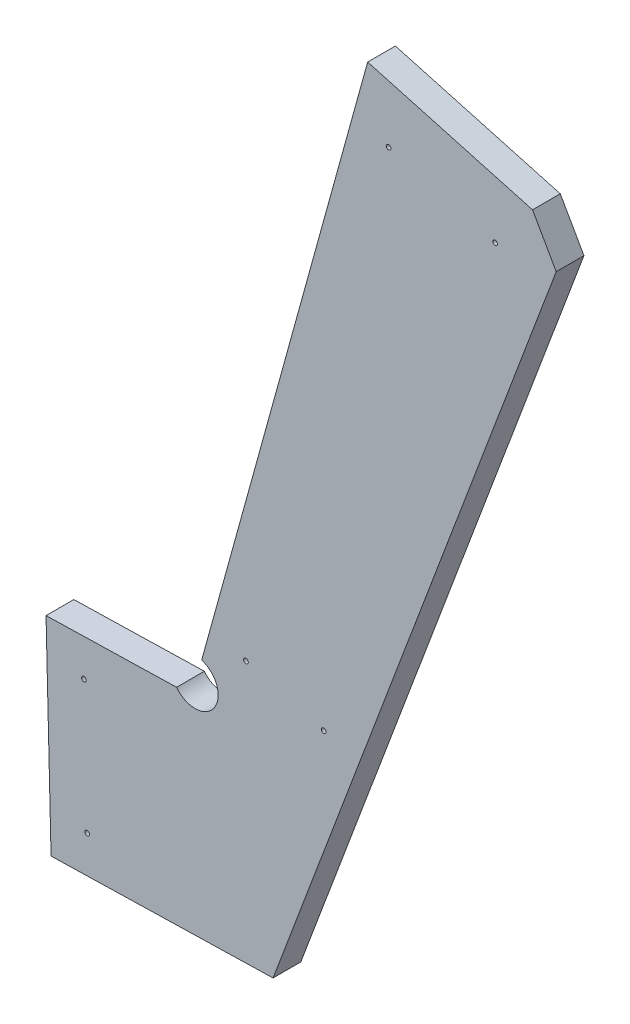
SolidWorks part; units mm, degrees
material "Beech"
ref_plane "Front Plane" through (0, 0, 0) normal (0, 0, 1) x (1, 0, 0)
ref_plane "Top Plane" through (0, 0, 0) normal (0, 1, 0) x (1, 0, 0)
ref_plane "Right Plane" through (0, 0, 0) normal (1, 0, 0) x (0, 0, -1)
sketch "Sketch1" plane through (0, 0, 0) normal (0, 0, 1) x (1, 0, 0)
  line L0 (-45.6457, -462.2836) -> (-42.1969, -603.5294)
  line L12 (288.249, -54.1429) -> (175.0934, -22.8896)
  line L13 (175.0934, -22.8896) -> (61.1778, -435.3327)
  line L14 (43.9506, -460.0959) -> (-45.6457, -462.2836)
  line L16 (-42.1969, -603.5294) -> (110.1577, -599.8093)
  line L17 (110.1577, -599.8093) -> (304.502, -82.7999)
  line L37 (304.502, -82.7999) -> (288.249, -54.1429)
  arc A2 (43.9506, -460.0959) -> (61.1778, -435.3327) centre (56.6289, -450.542) ccw
  dimension "D2" = 152.4
extrude "Boss-Extrude1" add sketch "Sketch1" along normal blind 19.05
hole_wizard "Hole1" positions "Sketch2" profile "Sketch3" legacy
sketch "Sketch2" plane through (162.2459, -21.7021, -146.425) normal (-0.9639, 0.2662, 0) x (0, 0, -1)
  line L8 (155.95, -2.2757) -> (155.95, 437.7664) construction
  line L11 (175, -2.2757) -> (175, 437.7664) construction
  line L15 (155.95, -2.2757) -> (155.95, 107.7348)
  line L16 (155.95, 107.7348) -> (155.95, 217.7454)
  line L17 (155.95, 217.7454) -> (155.95, 327.7559)
  line L18 (155.95, 327.7559) -> (155.95, 437.7664)
  line L20 (175, -2.2757) -> (175, 85.7327)
  line L21 (175, 85.7327) -> (175, 173.7411)
  line L22 (175, 173.7411) -> (175, 261.7496)
  line L23 (175, 261.7496) -> (175, 349.758)
  line L24 (175, 349.758) -> (175, 437.7664)
  line L25 (0, 155.0243) -> (0, 437.7664) construction
  point P36 (155.95, 107.7348)
  point P40 (155.95, 327.7559)
  point P46 (175, 85.7327)
  point P52 (175, 349.758)
  point P77 (-175, 349.758)
  point P80 (-175, 85.7327)
  point P81 (-155.95, 327.7559)
  point P83 (-155.95, 107.7348)
sketch "Sketch3" plane through (133.5638, -125.5487, 9.525) normal (0, 0, 1) x (-0.2662, -0.9639, 0)
  line L0 (0, 0) -> (0, 32.7039)
  line L1 (0, 32.7039) -> (1.5875, 31.75)
  line L2 (1.5875, 31.75) -> (1.5875, 4.0177)
  line L3 (1.5875, 4.0177) -> (5.08, 0)
  line L4 (5.08, 0) -> (0, 0)
  line L5 (0, -14.3089) -> (0, 102.4216) construction
  line L6 (0, 32.7039) -> (-1.5875, 31.75) construction
  line L7 (-1.5875, 4.0177) -> (-5.08, 0) construction
  dimension "Diameter" = 3.175
  dimension "Depth" = 31.75
  dimension "C-Sink Diameter" = 10.16
  dimension "C-Sink Angle" = 82
  dimension "Drill Angle" = 118
hole_wizard "Hole2" positions "Sketch4" profile "Sketch5" legacy
sketch "Sketch4" plane through (162.2459, -21.7021, 165.475) normal (-0.9639, 0.2662, 0) x (0, 0, -1)
  line L8 (155.95, -2.2757) -> (155.95, 437.7664) construction
  line L11 (175, -2.2757) -> (175, 437.7664) construction
  line L15 (155.95, -2.2757) -> (155.95, 107.7348)
  line L16 (155.95, 107.7348) -> (155.95, 217.7454)
  line L17 (155.95, 217.7454) -> (155.95, 327.7559)
  line L18 (155.95, 327.7559) -> (155.95, 437.7664)
  line L20 (175, -2.2757) -> (175, 85.7327)
  line L21 (175, 85.7327) -> (175, 173.7411)
  line L22 (175, 173.7411) -> (175, 261.7496)
  line L23 (175, 261.7496) -> (175, 349.758)
  line L24 (175, 349.758) -> (175, 437.7664)
  line L25 (0, 155.0243) -> (0, 437.7664) construction
  point P36 (155.95, 107.7348)
  point P40 (155.95, 327.7559)
  point P46 (175, 85.7327)
  point P52 (175, 349.758)
  point P77 (-175, 349.758)
  point P80 (-175, 85.7327)
  point P81 (-155.95, 327.7559)
  point P83 (-155.95, 107.7348)
sketch "Sketch5" plane through (133.5638, -125.5487, 321.425) normal (0, 0, 1) x (-0.2662, -0.9639, 0)
  line L0 (0, 0) -> (0, 32.7039)
  line L1 (0, 32.7039) -> (1.5875, 31.75)
  line L2 (1.5875, 31.75) -> (1.5875, 4.0177)
  line L3 (1.5875, 4.0177) -> (5.08, 0)
  line L4 (5.08, 0) -> (0, 0)
  line L5 (0, -14.3089) -> (0, 102.4216) construction
  line L6 (0, 32.7039) -> (-1.5875, 31.75) construction
  line L7 (-1.5875, 4.0177) -> (-5.08, 0) construction
  dimension "Diameter" = 3.175
  dimension "Depth" = 31.75
  dimension "C-Sink Diameter" = 10.16
  dimension "C-Sink Angle" = 82
  dimension "Drill Angle" = 118
hole_wizard "Hole3" positions "Sketch6" profile "Sketch7" legacy
sketch "Sketch6" plane through (311.9283, -63.0439, -19.05) normal (0, 0, -1) x (-0.3519, -0.9361, 0)
  line L0 (48.5061, 138.7859) -> (35.9701, 0) construction
  line L5 (414.5728, 105.7206) -> (405.0235, 0) construction
  line L7 (490.0108, 170.6797) -> (621.0107, 117.7523) construction
  line L12 (503.094, 203.0616) -> (634.0938, 150.1342) construction
  line L16 (586.8736, 410.4234) -> (717.8734, 357.496) construction
  line L19 (597.4602, 127.2674) -> (610.5433, 159.6493) construction
  line L20 (610.5433, 159.6493) -> (694.3229, 367.011) construction
  line L22 (513.5613, 161.1647) -> (526.6445, 193.5466) construction
  line L23 (526.6445, 193.5466) -> (610.424, 400.9084) construction
  point P0 (46.2211, 113.4889)
  point P2 (39.3976, 37.9455)
  point P4 (412.2879, 80.4236)
  point P51 (407.3085, 25.297)
  point P56 (513.5613, 161.1647)
  point P58 (597.4602, 127.2674)
  point P61 (610.5433, 159.6493)
  point P63 (694.3229, 367.011)
  point P66 (526.6445, 193.5466)
  point P68 (610.424, 400.9084)
sketch "Sketch7" plane through (189.4334, -66.3768, -19.05) normal (1, 0, 0) x (0, 1, 0)
  line L0 (0, 0) -> (0, 39.0539)
  line L1 (0, 39.0539) -> (1.5875, 38.1)
  line L2 (1.5875, 38.1) -> (1.5875, 4.0177)
  line L3 (1.5875, 4.0177) -> (5.08, 0)
  line L4 (5.08, 0) -> (0, 0)
  line L5 (0, -14.3089) -> (0, 102.4216) construction
  line L6 (0, 39.0539) -> (-1.5875, 38.1) construction
  line L7 (-1.5875, 4.0177) -> (-5.08, 0) construction
  dimension "Diameter" = 3.175
  dimension "Depth" = 38.1
  dimension "C-Sink Diameter" = 10.16
  dimension "C-Sink Angle" = 82
  dimension "Drill Angle" = 118
